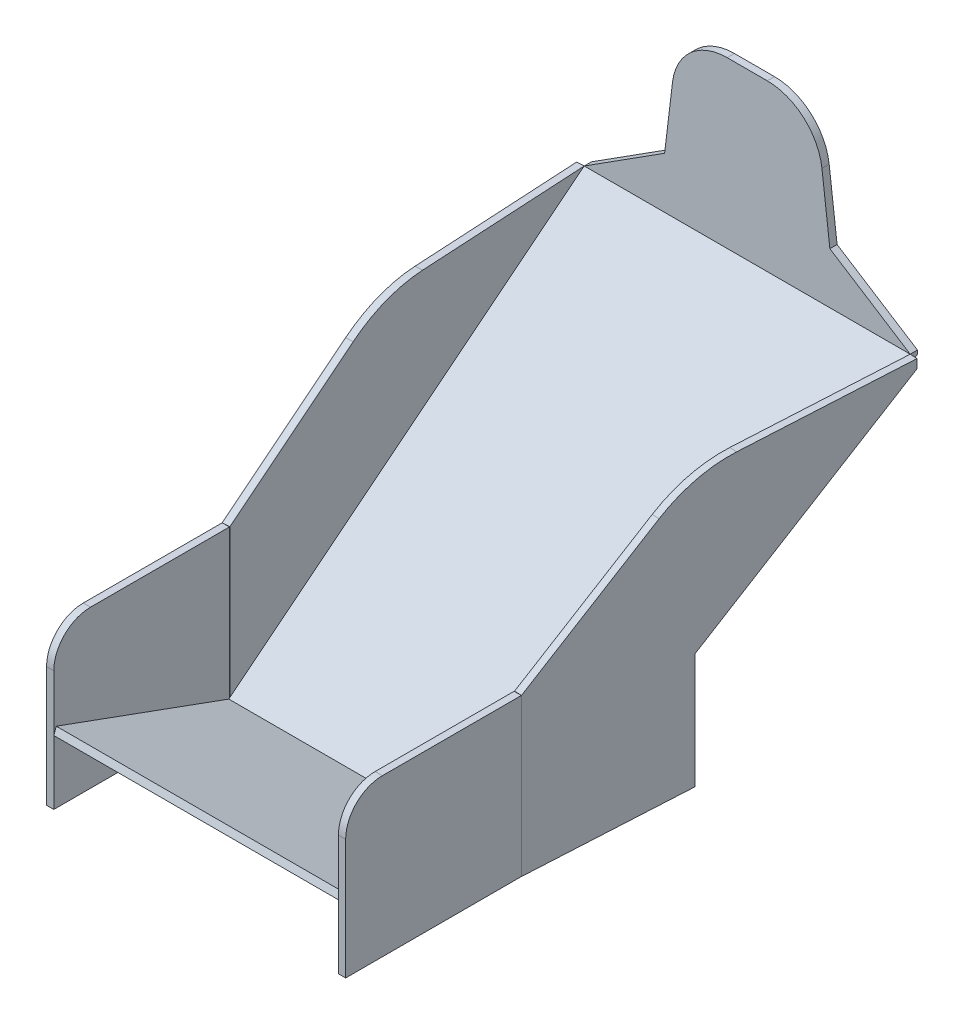
SolidWorks part; units mm, degrees
other "Markup1"
sketch "Sketch12" plane through (517.9841, 348.8096, 415.0532) normal (0.7189, 0.5821, 0.3799) x (0.3604, 0.1552, -0.9198)
other "Markup2"
sketch "Sketch13" plane through (460.8349, 243.4719, 415.0532) normal (0.2146, 0.3678, 0.9048) x (0.9597, 0.0928, -0.2654)
material "Corrugated Paper"
ref_plane "Front Plane" through (0, 0, 0) normal (0, 0, 1) x (1, 0, 0)
ref_plane "Top Plane" through (0, 0, 0) normal (0, 1, 0) x (1, 0, 0)
ref_plane "Right Plane" through (0, 0, 0) normal (1, 0, 0) x (0, 0, -1)
sketch "Sketch1" plane through (0, 0, 0) normal (1, 0, 0) x (0, 0, -1)
  line L0 (-172.9511, -349.3491) -> (-411.633, -262.476)
  line L1 (-172.9511, -349.3491) -> (347.2104, 14.8719)
  line L2 (347.2104, 14.8719) -> (347.2104, 243.4719)
  line L3 (-171.4796, -360.5265) -> (-415.0532, -271.8729)
  line L4 (-171.4796, -360.5265) -> (357.2104, 9.6662)
  line L5 (357.2104, 9.6662) -> (357.2104, 243.4719)
  line L6 (-411.633, -262.476) -> (-415.0532, -271.8729)
  line L7 (357.2104, 243.4719) -> (347.2104, 243.4719)
  dimension "D1" = 254
  dimension "D2" = 635
  dimension "D3" = 228.6
  dimension "D4" = 125
  dimension "D6" = 125
  dimension "D5" = 10
extrude "Boss-Extrude1" add sketch "Sketch1" along normal blind 450.85
sketch "Sketch3" plane through (0, 0, -347.2104) normal (0, 0, 1) x (1, 0, 0)
  line L1 (450.85, 243.4719) -> (0, 243.4719) construction
  line L2 (130.175, 243.4719) -> (320.675, 243.4719)
  line L4 (450.85, 243.4719) -> (450.85, 14.8719) construction
  line L5 (450.85, 14.8719) -> (0, 14.8719) construction
  line L6 (450.85, 14.8719) -> (450.85, 243.4719)
  line L7 (450.85, 243.4719) -> (320.675, 243.4719)
  line L8 (0, 14.8719) -> (0, 243.4719)
  line L9 (0, 243.4719) -> (0, 14.8719) construction
  line L10 (0, 243.4719) -> (130.175, 243.4719)
  line L11 (130.175, 243.4719) -> (111.125, 85.6505)
  line L12 (111.125, 85.6505) -> (0, 14.8719)
  line L13 (320.675, 243.4719) -> (339.725, 85.6505)
  line L14 (339.725, 85.6505) -> (450.85, 14.8719)
  point P20 (225.425, 243.4719)
  line M12 (0, 243.4719) -> (0, 14.8719)
  line M14 (450.85, 14.8719) -> (450.85, 243.4719)
  line M15 (450.85, 243.4719) -> (0, 243.4719)
  dimension "D1" = 190.5
  dimension "D2" = 130.175
  dimension "D3" = 228.6
  dimension "D4" = 114.3
extrude "Cut-Extrude2" cut sketch "Sketch3" against normal blind 508 contours L13 L14 M14 M15 | L12 L11 M15 M12
fillet "Fillet1" radius 76.2 2 edges at (130.175, 243.4719, -352.2104) (320.675, 243.4719, -352.2104)
sketch "Sketch8" plane through (0, 0, 0) normal (0, 1, 0) x (1, 0, 0)
  line L0 (0, 347.2104) -> (28.575, -172.9511)
  line L1 (450.85, -172.9511) -> (0, -172.9511) construction
  line L2 (28.575, -172.9511) -> (0, -172.9511)
  line L3 (0, -172.9511) -> (0, 347.2104)
  line L4 (450.85, 347.2104) -> (422.275, -172.9511)
  line L5 (422.275, -172.9511) -> (450.85, -172.9511)
  line L6 (450.85, -172.9511) -> (450.85, 347.2104)
  line L7 (28.575, -172.9511) -> (28.575, -423.4668)
  line L8 (28.575, -423.4668) -> (0, -423.4668)
  line L9 (0, -423.4668) -> (0, -172.9511)
  line L10 (422.275, -172.9511) -> (422.275, -423.4668)
  line L11 (422.275, -423.4668) -> (450.85, -423.4668)
  line L12 (450.85, -423.4668) -> (450.85, -172.9511)
  point P17 (225.425, -172.9511)
  dimension "D1" = 196.85
  dimension "D2" = 393.7
extrude "Cut-Extrude3" cut sketch "Sketch8" against normal through all and the other way through all contours L3 L2 L0 | L5 L6 L4 | L11 L12 L5 L10 | L9 L8 L7 L2
sketch "Sketch9" plane through (19.0166, 0, -1.0447) normal (-0.9985, 0, 0.0549) x (0.0549, 0, 0.9985)
  line L0 (-346.6877, 14.8719) -> (-53.8499, 14.8719)
  line L1 (-53.8499, 14.8719) -> (172.7844, -143.5802)
  line L2 (172.7844, -143.5802) -> (172.7844, -360.5265)
  line L3 (172.7844, -360.5265) -> (-346.6877, 2.6642)
  line L4 (-346.6877, 2.6642) -> (172.7844, -360.5265) construction
  line L5 (-346.6877, 2.6642) -> (-346.6877, 14.8719)
  line L7 (174.2581, -349.3491) -> (-346.6877, 14.8719) construction
  line L8 (-55.253, -201.0934) -> (-55.253, -360.5265)
  line L9 (-55.253, -360.5265) -> (172.7844, -360.5265)
  line L10 (-346.6877, 2.6642) -> (-346.6877, 14.8719) construction
  line M6 (174.2581, -349.3491) -> (-346.6877, 14.8719)
  line M7 (-346.6877, 14.8719) -> (-346.6877, 2.6642)
  line M8 (-346.6877, 2.6642) -> (172.7844, -360.5265)
  dimension "D1" = 177.8
  dimension "D2" = 355.6
extrude "Boss-Extrude4" add sketch "Sketch9" along normal blind 10 contours L2 L1 L0 M6 | L8 L9 L3 | L2 L3 M6 M7 M8
sketch "Sketch11" plane through (28.575, 0, 0) normal (-1, 0, 0) x (0, 0, 1)
  line L0 (-55.6659, -360.5265) -> (172.0281, -360.5265) construction
  line L1 (172.0281, -143.5802) -> (415.0532, -143.5802)
  line L2 (172.0281, -143.5802) -> (172.0281, -360.5265)
  line L3 (172.0281, -360.5265) -> (415.0532, -360.5265)
  line L4 (415.0532, -143.5802) -> (415.0532, -360.5265)
extrude "Boss-Extrude5" add sketch "Sketch11" along normal blind 10
fillet "Fillet2" radius 177.8 1 edges at (11.0703, 14.8719, -54.5393)
fillet "Fillet3" radius 50.8 1 edges at (23.575, -143.5802, 415.0532)
ref_plane "Plane1" through (225.425, 0, 0) normal (1, 0, 0) x (0, 0, -1)
mirror "Mirror1" about plane through (225.425, 0, 0) normal (1, 0, 0) of "Boss-Extrude4", "Boss-Extrude5", "Fillet2", "Fillet3"
